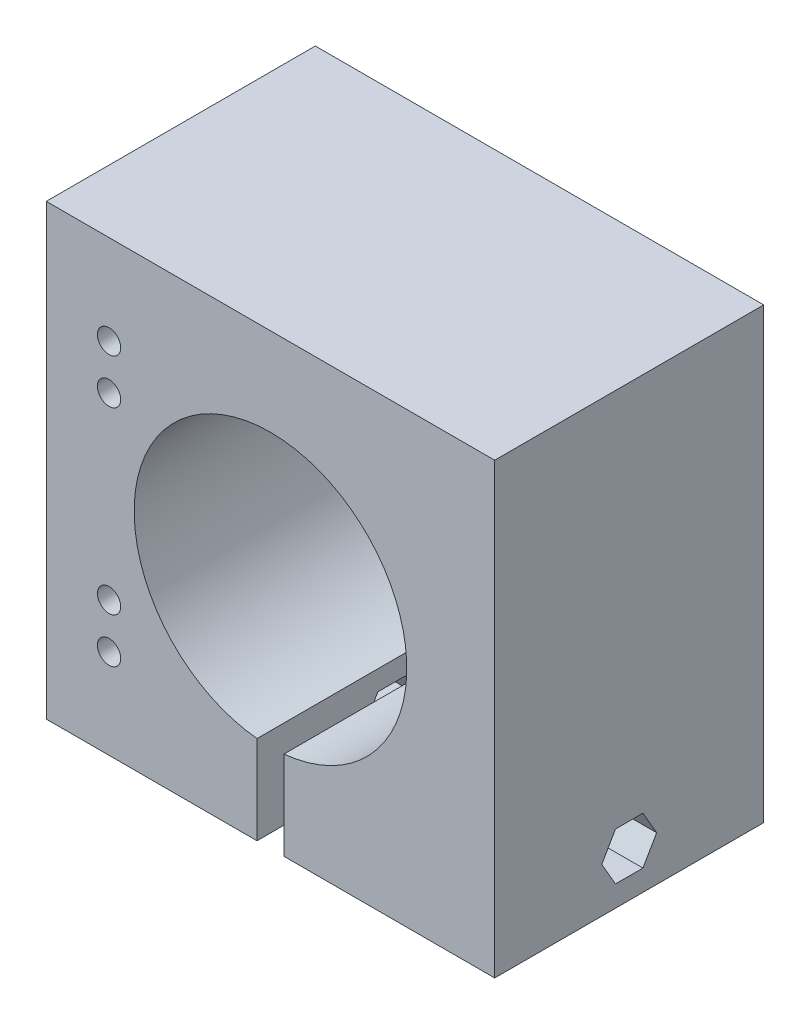
SolidWorks part; units mm, degrees
ref_plane "Front Plane" through (0, 0, 0) normal (0, 0, 1) x (1, 0, 0)
ref_plane "Top Plane" through (0, 0, 0) normal (0, 1, 0) x (1, 0, 0)
ref_plane "Right Plane" through (0, 0, 0) normal (1, 0, 0) x (0, 0, -1)
sketch "Sketch1" plane through (0, 0, 0) normal (0, 0, 1) x (1, 0, 0)
  line L1 (0, 0) -> (50, 0)
  line L2 (0, 0) -> (0, 50)
  line L3 (0, 50) -> (50, 50)
  line L4 (50, 0) -> (50, 50)
  circle A0 centre (25, 25) radius 15.2
  circle A1 centre (7, 15) radius 1.3
  circle A2 centre (7, 40) radius 1.3
  circle A3 centre (7, 10) radius 1.3
  circle A4 centre (7, 35) radius 1.3
  dimension "D3" = 30.4
  dimension "D6" = 5
  dimension "D7" = 2.6
  dimension "D14" = 18
  dimension "D8" = 2.6
  dimension "D1" = 50
  dimension "D2" = 50
  dimension "D4" = 25
  dimension "D5" = 25
  dimension "D9" = 5
  dimension "D11" = 10
  dimension "D12" = 10
  dimension "D13" = 18
extrude "Boss-Extrude1" add sketch "Sketch1" along normal blind 30
sketch "Sketch2" plane through (0, 0, 30) normal (0, 0, 1) x (1, 0, 0)
  line L0 (0, 0) -> (50, 0) construction
  line L1 (23.5, 0) -> (26.5, 0)
  line L2 (23.5, 0) -> (23.5, 11.7091)
  line L3 (23.5, 11.7091) -> (26.5, 11.7091)
  line L4 (26.5, 0) -> (26.5, 11.7091)
  line L5 (50, 0) -> (50, 50) construction
  dimension "D1" = 3
  dimension "D2" = 23.5
extrude "Cut-Extrude1" cut sketch "Sketch2" against normal up to next
sketch "Sketch3" plane through (50, 0, 0) normal (1, 0, 0) x (0, 0, -1)
  line L2 (-13.47, 7.65) -> (-16.53, 2.35) construction
  line L3 (-11.94, 5) -> (-13.47, 7.65)
  line L4 (-13.47, 7.65) -> (-16.53, 7.65)
  line L5 (-16.53, 7.65) -> (-18.06, 5)
  line L6 (-18.06, 5) -> (-16.53, 2.35)
  line L7 (-16.53, 2.35) -> (-13.47, 2.35)
  line L8 (-13.47, 2.35) -> (-11.94, 5)
  line L9 (0, 0) -> (0, 50) construction
  line L10 (-30, 0) -> (0, 0) construction
  point P0 (-15, 5)
  dimension "D1" = 15
  dimension "D2" = 5
  dimension "D4" = 5.3
extrude "Cut-Extrude2" cut sketch "Sketch3" against normal blind 54
sketch "Sketch4" plane through (0, 0, 0) normal (-1, 0, 0) x (0, 0, 1)
  line L1 (19.792, 5) -> (17.396, 9.15)
  line L2 (17.396, 9.15) -> (12.604, 9.15)
  line L3 (12.604, 9.15) -> (10.208, 5)
  line L4 (10.208, 5) -> (12.604, 0.85)
  line L5 (12.604, 0.85) -> (17.396, 0.85)
  line L6 (17.396, 0.85) -> (19.792, 5)
  dimension "D1" = 8.3
extrude "Cut-Extrude3" cut sketch "Sketch4" against normal blind 5
